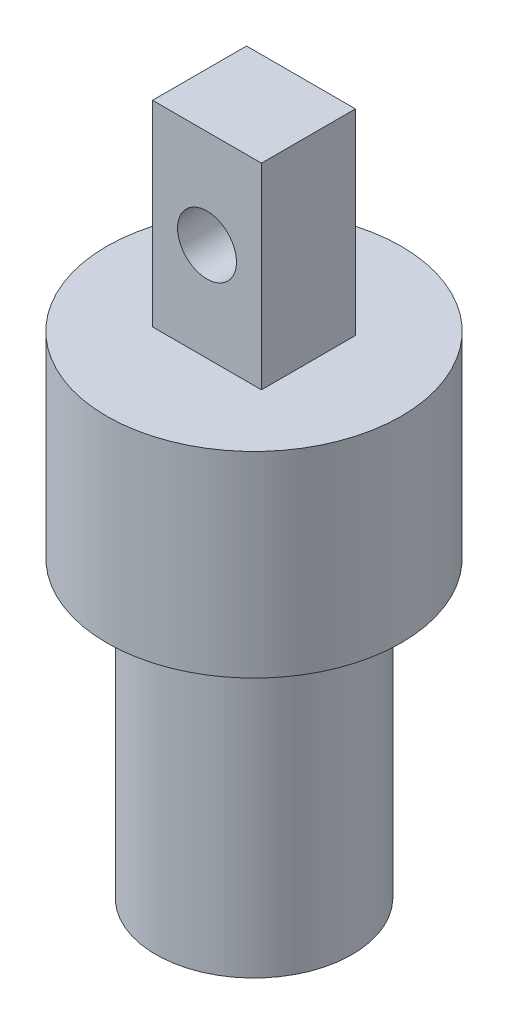
SolidWorks part; units mm, degrees
ref_plane "Front Plane" through (0, 0, 0) normal (0, 0, 1) x (1, 0, 0)
ref_plane "Top Plane" through (0, 0, 0) normal (0, 1, 0) x (1, 0, 0)
ref_plane "Right Plane" through (0, 0, 0) normal (1, 0, 0) x (0, 0, -1)
sketch "Sketch1" plane through (0, 0, 0) normal (0, 1, 0) x (1, 0, 0)
  circle A0 centre (0, 0) radius 7.5
  dimension "D1" = 15
extrude "Boss-Extrude1" add sketch "Sketch1" along normal blind 10
sketch "Sketch2" plane through (0, 10, 0) normal (0, 1, 0) x (1, 0, 0)
  line L1 (-2.7737, -2.3941) -> (2.7737, -2.3941)
  line L2 (-2.7737, -2.3941) -> (-2.7737, 2.3941)
  line L3 (-2.7737, 2.3941) -> (2.7737, 2.3941)
  line L4 (2.7737, -2.3941) -> (2.7737, 2.3941)
  line L5 (-2.7737, -2.3941) -> (2.7737, 2.3941) construction
  line L6 (-2.7737, 2.3941) -> (2.7737, -2.3941) construction
  point P0 (0, 0)
extrude "Boss-Extrude2" add sketch "Sketch2" along normal blind 10
sketch "Sketch4" plane through (0, 0, -2.3941) normal (0, 0, -1) x (-1, 0, 0)
  line L0 (-2.7737, 10) -> (2.7737, 10) construction
  circle A0 centre (0, 15) radius 1.5
  dimension "D1" = 3
  dimension "D2" = 5
extrude "Cut-Extrude1" cut sketch "Sketch4" against normal blind 10
sketch "Sketch5" plane through (0, 0, 0) normal (0, -1, 0) x (-1, 0, 0)
  circle A0 centre (0, 0) radius 5
  dimension "D1" = 10
extrude "Boss-Extrude3" add sketch "Sketch5" along normal blind 15
